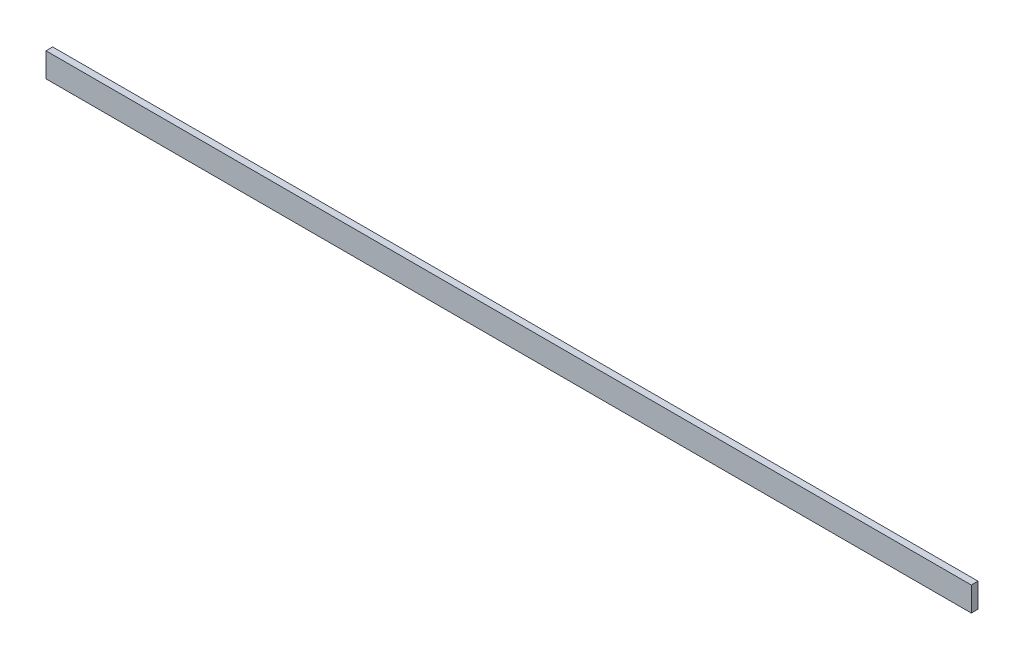
SolidWorks part; units mm, degrees
ref_plane "Face" through (0, 0, 0) normal (0, 0, 1) x (1, 0, 0)
ref_plane "Dessus" through (0, 0, 0) normal (0, 1, 0) x (1, 0, 0)
ref_plane "Droite" through (0, 0, 0) normal (1, 0, 0) x (0, 0, -1)
sketch "Esquisse1" plane through (0, 0, 0) normal (0, 0, 1) x (1, 0, 0)
  line L1 (0, 0) -> (3044, 0)
  line L2 (0, 0) -> (0, 80)
  line L3 (0, 80) -> (3044, 80)
  line L4 (3044, 0) -> (3044, 80)
  dimension "D1" = 3044
  dimension "D2" = 80
extrude "Extrusion1" add sketch "Esquisse1" along normal blind 22
